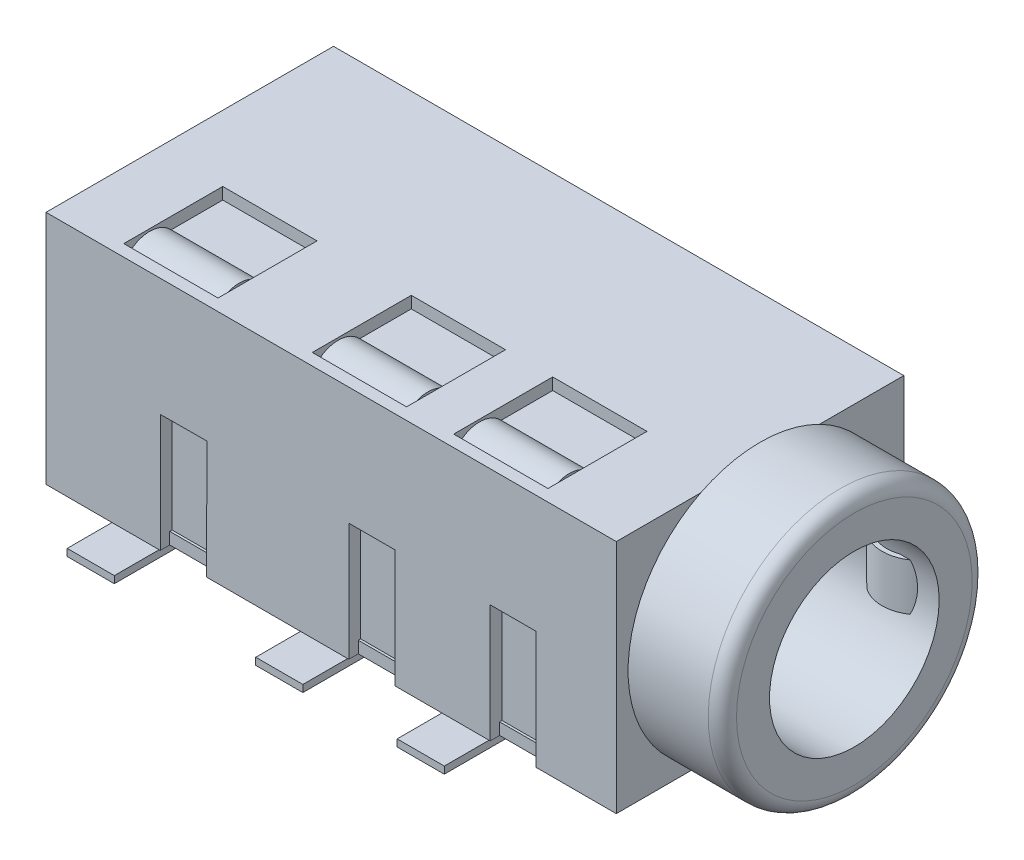
SolidWorks part; units mm, degrees
ref_plane "Front Plane" through (0, 0, 0) normal (0, 0, 1) x (1, 0, 0)
ref_plane "Top Plane" through (0, 0, 0) normal (0, 1, 0) x (1, 0, 0)
ref_plane "Right Plane" through (0, 0, 0) normal (1, 0, 0) x (0, 0, -1)
sketch "Sketch1" plane through (0, 0, 0) normal (0, 1, 0) x (1, 0, 0)
  line L0 (0, 0) -> (0, 6.1)
  line L1 (0, 6.1) -> (12.1, 6.1)
  line L2 (0, 0) -> (12.1, 0)
  line L3 (12.1, 0) -> (12.1, 6.1)
extrude "Boss-Extrude1" add sketch "Sketch1" along normal blind 5
sketch "Sketch2" plane through (12.1, 0, 0) normal (1, 0, 0) x (0, 0, -1)
  line L1 (0, 5) -> (0, 0) construction
  circle A0 centre (3.05, 2.5) radius 2.8
extrude "Boss-Extrude2" add sketch "Sketch2" along normal blind 2
sketch "Sketch3" plane through (14.1, 0, 0) normal (1, 0, 0) x (0, 0, -1)
  circle A0 centre (3.05, 2.5) radius 1.8
extrude "Cut-Extrude1" cut sketch "Sketch3" against normal blind 14
sketch "Sketch4" plane through (0, 0, 0) normal (0, -1, 0) x (1, 0, 0)
  line L3 (6.4, -1.05) -> (5.4, -1.05)
  line L4 (5.4, -1.05) -> (5.4, 0.95)
  line L6 (9.4, -1.05) -> (8.4, -1.05)
  line L7 (8.4, -1.05) -> (8.4, 0.95)
  line L8 (9.4, 0.95) -> (9.4, -1.05)
  line L9 (8.4, 0.95) -> (9.4, 0.95)
  line L10 (6.4, 0.95) -> (6.4, -1.05)
  line L11 (5.4, 0.95) -> (6.4, 0.95)
  line L12 (2.4, -1.05) -> (1.4, -1.05)
  line L13 (1.4, -1.05) -> (1.4, 0.95)
  line L14 (2.4, 0.95) -> (2.4, -1.05)
  line L15 (1.4, 0.95) -> (2.4, 0.95)
  line L17 (1.9048, -7.05) -> (0.9048, -7.05)
  line L18 (0.9048, -7.05) -> (0.9048, -5.05)
  line L19 (1.9048, -5.05) -> (1.9048, -7.05)
  line L20 (0.9048, -5.05) -> (1.9048, -5.05)
extrude "Boss-Extrude3" add sketch "Sketch4" along normal blind 0.15
sketch "Sketch5" plane through (0, 0, 0) normal (0, 0, 1) x (1, 0, 0)
  line L0 (3.4, 0) -> (3.4198, 2.5)
  line L2 (9.425, 2.5) -> (10.4, 2.5)
  line L4 (9.425, 2.5) -> (9.425, 0)
  line L5 (2.425, 2.5) -> (3.4203, 2.5044)
  line L6 (6.425, 2.5) -> (7.4, 2.5)
  line L7 (6.425, 2.5) -> (6.425, 0)
  line L8 (7.4, 2.5) -> (7.4, 0)
  line L9 (6.4, 0) -> (8.4, 0) construction
  line L10 (2.425, 0) -> (3.4, 0)
  line L11 (2.425, 0) -> (2.425, 2.5)
  line L12 (6.425, 0) -> (7.4, 0)
  line L13 (10.4, 2.5) -> (10.4, 0)
  line L14 (9.4, 0) -> (12.1, 0) construction
  line L15 (3.4198, 2.5) -> (3.4203, 2.5044)
  line L18 (9.425, 0) -> (10.4, 0)
extrude "Cut-Extrude2" cut sketch "Sketch5" against normal blind 0.25
sketch "Sketch7" plane through (0, 0, -6.1) normal (0, 0, -1) x (-1, 0, 0)
  line L0 (-2.9048, 2.5) -> (-1.9298, 2.5)
  line L2 (-12.1, 0) -> (-1.9048, 0) construction
  line L3 (-2.9048, 0) -> (-2.9048, 2.5)
  line L4 (-1.9298, 2.5) -> (-1.9298, 0)
  line L5 (-2.9048, 0) -> (-1.9298, 0)
extrude "Cut-Extrude4" cut sketch "Sketch7" against normal blind 0.25
sketch "Sketch8" plane through (0, 5, 0) normal (0, 1, 0) x (1, 0, 0)
  line L2 (3.4, 0.25) -> (1.4, 0.25)
  line L4 (1.4, 2.35) -> (1.4, 0.25)
  line L6 (7.4, 0.25) -> (5.4, 0.25)
  line L7 (1.4, 2.35) -> (3.4, 2.35)
  line L8 (3.4, 2.35) -> (3.4, 0.25)
  line L9 (5.4, 2.35) -> (5.4, 0.25)
  line L10 (5.4, 2.35) -> (7.4, 2.35)
  line L11 (7.4, 2.35) -> (7.4, 0.25)
  line L12 (10.4, 0.25) -> (8.4, 0.25)
  line L13 (8.4, 2.35) -> (8.4, 0.25)
  line L14 (8.4, 2.35) -> (10.4, 2.35)
  line L15 (10.4, 2.35) -> (10.4, 0.25)
extrude "Cut-Extrude5" cut sketch "Sketch8" against normal blind 0.25
sketch "Sketch10" plane through (12.1, 0, 0) normal (1, 0, 0) x (0, 0, -1)
  arc A0 (0.25, 4.7476) -> (1.2495, 4.7476) centre (0.7498, 4.379) cw
extrude "Extrude-Thin1" add sketch "Sketch10" against normal blind 1.9 from offset 1.75 separate body thin offset against normal yes
pattern_linear "LPattern1" count 2 spacing 3 along (-1, 0, 0) of "Extrude-Thin1"
pattern_linear "LPattern2" count 2 spacing 7 along (-1, 0, 0) of "Extrude-Thin1"
sketch "Sketch13" plane through (0, 0, -0.25) normal (0, 0, 1) x (1, 0, 0)
  line L0 (2.4, 0) -> (2.4, 0.25)
  line L1 (2.4, 2.5) -> (2.4, 0) construction
  line L2 (2.4, 0.25) -> (3.402, 0.25)
  line L3 (3.4, 0) -> (3.4198, 2.5) construction
  line L4 (3.402, 0.25) -> (3.4, 0)
  line L5 (2.425, 0) -> (3.4, 0) construction
  line L6 (3.4, 0) -> (2.4, 0)
  line L7 (6.4, 0) -> (6.4, 0.25)
  line L8 (6.4, 2.5) -> (6.4, 0) construction
  line L9 (6.4, 0.25) -> (7.4, 0.25)
  line L10 (7.4, 0) -> (7.4, 2.5) construction
  line L11 (7.4, 0.25) -> (7.4, 0)
  line L12 (7.4, 0) -> (6.4, 0)
  line L13 (9.4, 0) -> (9.4, 0.25)
  line L14 (9.4, 2.5) -> (9.4, 0) construction
  line L15 (9.4, 0.25) -> (10.4, 0.25)
  line L16 (10.4, 0) -> (10.4, 2.5) construction
  line L17 (10.4, 0.25) -> (10.4, 0)
  line L18 (10.4, 0) -> (9.4, 0)
extrude "Boss-Extrude4" add sketch "Sketch13" along normal blind 0.05
sketch "Sketch14" plane through (0, 0, -5.85) normal (0, 0, -1) x (-1, 0, 0)
  line L0 (-2.9048, 0) -> (-2.9048, 0.25)
  line L1 (-2.9048, 2.5) -> (-2.9048, 0) construction
  line L2 (-2.9048, 0.25) -> (-1.9048, 0.25)
  line L3 (-1.9048, 0) -> (-1.9048, 2.5) construction
  line L4 (-1.9048, 0.25) -> (-1.9048, 0)
  line L5 (-1.9048, 0) -> (-2.9048, 0)
extrude "Boss-Extrude5" add sketch "Sketch14" along normal blind 0.05
fillet "Fillet1" radius 0.3 1 edges at (14.1, 2.5, -5.85)
sketch "Sketch15" plane through (0, 5, 0) normal (0, 1, 0) x (1, 0, 0)
  arc A0 (12.5965, 4.9472) -> (13.5997, 4.9472) centre (13.0981, 5.4488) ccw
extrude "Extrude-Thin3" add sketch "Sketch15" along normal blind 1 from offset 3 thin offset against normal yes
